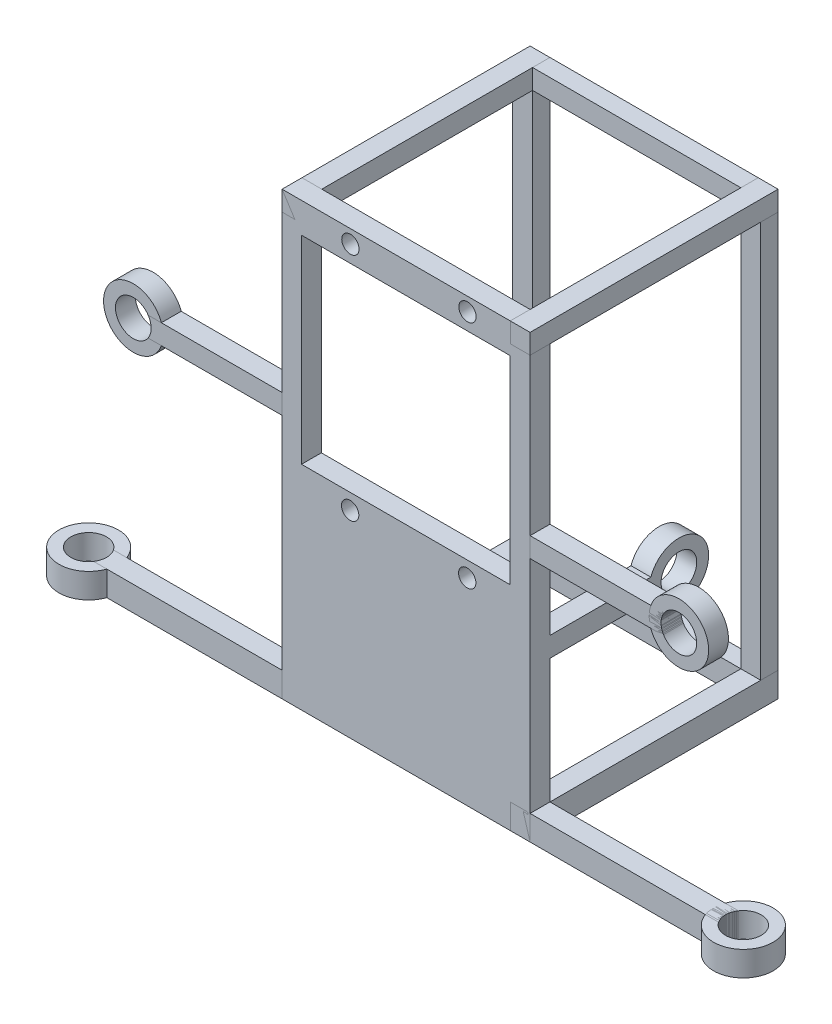
SolidWorks part; units mm, degrees
ref_plane "Front Plane" through (0, 0, 0) normal (0, 0, 1) x (1, 0, 0)
ref_plane "Top Plane" through (0, 0, 0) normal (0, 1, 0) x (1, 0, 0)
ref_plane "Right Plane" through (0, 0, 0) normal (1, 0, 0) x (0, 0, -1)
sketch "Sketch114" plane through (0, 0, 0) normal (1, 0, 0) x (0, 0, -1)
  line L1 (0, 0) -> (3.5, 0)
  line L2 (0, 0) -> (0, 80)
  line L3 (0, 80) -> (3.5, 80)
  line L4 (3.5, 0) -> (3.5, 80)
extrude "Boss-Extrude2" add sketch "Sketch114" along normal blind 4
sketch "Sketch115" plane through (0, 80, 0) normal (0, 1, 0) x (1, 0, 0)
  line L1 (0, 0) -> (50, 0)
  line L2 (0, 0) -> (0, 3.5)
  line L3 (0, 3.5) -> (50, 3.5)
  line L4 (50, 0) -> (50, 3.5)
extrude "Boss-Extrude3" add sketch "Sketch115" along normal blind 4 separate body
sketch "Sketch116" plane through (50, 0, 0) normal (1, 0, 0) x (0, 0, -1)
  line L1 (3.5, 80) -> (0, 80)
  line L2 (3.5, 80) -> (3.5, 0)
  line L3 (3.5, 0) -> (0, 0)
  line L4 (0, 80) -> (0, 0)
extrude "Boss-Extrude5" add sketch "Sketch116" against normal blind 4 separate body
sketch "Sketch117" plane through (0, 0, 0) normal (0, -1, 0) x (1, 0, 0)
  line L0 (0, 0) -> (0, -3.5) construction
  line L1 (0, -3.5) -> (50, -3.5)
  line L2 (0, -3.5) -> (0, 0)
  line L3 (0, 0) -> (50, 0)
  line L4 (50, -3.5) -> (50, 0)
extrude "Boss-Extrude6" add sketch "Sketch117" along normal blind 5 separate body contours L3 L4 L1 L2
sketch "Sketch119" plane through (50, 0, 0) normal (1, 0, 0) x (0, 0, -1)
  line L1 (3.5, -5) -> (-46.5, -5)
  line L2 (3.5, -5) -> (3.5, 0)
  line L3 (3.5, 0) -> (-46.5, 0)
  line L4 (-46.5, -5) -> (-46.5, 0)
  line L5 (3.5, 84) -> (-46.5, 84)
  line L6 (3.5, 84) -> (3.5, 80)
  line L7 (3.5, 80) -> (-46.5, 80)
  line L8 (-46.5, 84) -> (-46.5, 80)
extrude "Boss-Extrude7" add sketch "Sketch119" against normal blind 4 separate body
sketch "Sketch122" plane through (0, 0, 0) normal (-1, 0, 0) x (0, 0, 1)
  line L1 (-3.5, 84) -> (46.5, 84)
  line L2 (-3.5, 84) -> (-3.5, 80)
  line L3 (-3.5, 80) -> (46.5, 80)
  line L4 (46.5, 84) -> (46.5, 80)
  line L5 (-3.5, -5) -> (46.5, -5)
  line L6 (-3.5, -5) -> (-3.5, 0)
  line L7 (-3.5, 0) -> (46.5, 0)
  line L8 (46.5, -5) -> (46.5, 0)
extrude "Boss-Extrude8" add sketch "Sketch122" against normal blind 4 separate body
sketch "Sketch134" plane through (0, 0, 46.5) normal (0, 0, 1) x (1, 0, 0)
  line L1 (0, -5) -> (50, -5)
  line L2 (0, -5) -> (0, 84)
  line L3 (0, 84) -> (50, 84)
  line L4 (50, -5) -> (50, 84)
extrude "Boss-Extrude18" add sketch "Sketch134" against normal blind 4 separate body
sketch "Sketch135" plane through (0, -5, 0) normal (0, -1, 0) x (-1, 0, 0)
  line L1 (-46, -46.5) -> (-91, -46.5)
  line L2 (-46, -46.5) -> (-46, -42.5)
  line L3 (-46, -42.5) -> (-91, -42.5)
  line L4 (-91, -46.5) -> (-91, -42.5)
extrude "Boss-Extrude19" add sketch "Sketch135" against normal blind 5 separate body
sketch "Sketch136" plane through (0, -5, 0) normal (0, -1, 0) x (1, 0, 0)
  line L1 (4, 46.5) -> (-41, 46.5)
  line L2 (4, 46.5) -> (4, 42.5)
  line L3 (4, 42.5) -> (-41, 42.5)
  line L4 (-41, 46.5) -> (-41, 42.5)
extrude "Boss-Extrude21" add sketch "Sketch136" against normal blind 5 separate body
sketch "Sketch137" plane through (0, -5, 0) normal (0, -1, 0) x (1, 0, 0)
  line L0 (91, 42.5) -> (91, 46.5) construction
  circle A0 centre (91, 44.5) radius 6
extrude "Boss-Extrude22" add sketch "Sketch137" against normal blind 5 separate body
sketch "Sketch139" plane through (0, -5, 0) normal (0, -1, 0) x (-1, 0, 0)
  line L0 (-91, -42.5) -> (-91, -46.5) construction
  circle A0 centre (-91, -44.5) radius 3.6
extrude "Cut-Extrude1" cut sketch "Sketch139" against normal blind 38 and the other way blind 10
sketch "Sketch140" plane through (0, -5, 0) normal (0, -1, 0) x (1, 0, 0)
  line L0 (-41, 46.5) -> (-41, 42.5) construction
  circle A0 centre (-41, 44.5) radius 6
extrude "Boss-Extrude23" add sketch "Sketch140" against normal blind 5 separate body
sketch "Sketch143" plane through (0, -5, 0) normal (0, -1, 0) x (1, 0, 0)
  circle A0 centre (-41, 44.5) radius 3.6
extrude "Cut-Extrude2" cut sketch "Sketch143" against normal blind 17 and the other way blind 29
sketch "Sketch145" plane through (0, 5, 42.5) normal (0, 0, -1) x (-1, 0, 0)
  line L1 (0, 39.5) -> (30, 39.5)
  line L2 (0, 39.5) -> (0, 43.5)
  line L3 (0, 43.5) -> (30, 43.5)
  line L4 (30, 39.5) -> (30, 43.5)
extrude "Boss-Extrude26" add sketch "Sketch145" against normal blind 4 separate body contours L4 L3 L2 L1
sketch "Sketch146" plane through (0, 5, 46.5) normal (0, 0, 1) x (1, 0, 0)
  line L0 (-30, 39.5) -> (-30, 43.5) construction
  circle A0 centre (-30, 41.5) radius 6
extrude "Boss-Extrude27" add sketch "Sketch146" against normal blind 4 separate body
sketch "Sketch147" plane through (0, 5, 46.5) normal (0, 0, 1) x (1, 0, 0)
  circle A0 centre (-30, 41.5) radius 3.6
extrude "Cut-Extrude3" cut sketch "Sketch147" against normal blind 21 and the other way blind 11
sketch "Sketch148" plane through (0, 5, 46.5) normal (0, 0, 1) x (1, 0, 0)
  line L1 (50, 39.5) -> (80, 39.5)
  line L2 (50, 39.5) -> (50, 43.5)
  line L3 (50, 43.5) -> (80, 43.5)
  line L4 (80, 39.5) -> (80, 43.5)
extrude "Boss-Extrude28" add sketch "Sketch148" against normal blind 4 separate body
sketch "Sketch149" plane through (0, 5, 42.5) normal (0, 0, -1) x (-1, 0, 0)
  line L0 (-80, 39.5) -> (-80, 43.5) construction
  circle A0 centre (-80, 41.5) radius 6
extrude "Boss-Extrude29" add sketch "Sketch149" against normal blind 4 separate body
sketch "Sketch150" plane through (0, 5, 46.5) normal (0, 0, 1) x (1, 0, 0)
  line L0 (80, 39.5) -> (80, 43.5) construction
  circle A0 centre (80, 41.5) radius 3.6
extrude "Cut-Extrude4" cut sketch "Sketch150" along normal blind 12 and the other way blind 14
sketch "Sketch155" plane through (0, 0, 42.5) normal (0, 0, -1) x (-1, 0, 0)
sketch "Sketch156" plane through (0, 0, 46.5) normal (0, 0, 1) x (1, 0, 0)
  line L1 (3.9148, 77.9202) -> (45.9148, 77.9202)
  line L2 (3.9148, 77.9202) -> (3.9148, -0.0798)
  line L3 (3.9148, -0.0798) -> (45.9148, -0.0798)
  line L4 (45.9148, 77.9202) -> (45.9148, -0.0798)
extrude "Cut-Extrude8" cut sketch "Sketch156" against normal blind 4
sketch "Sketch159" plane through (50, 0, 0) normal (1, 0, 0) x (0, 0, -1)
  line L0 (-46.5, -5) -> (-46.5, 84) construction
  line L1 (-46.5, 29.085) -> (-16.5, 29.085)
  line L2 (-46.5, 29.085) -> (-46.5, 25.085)
  line L3 (-46.5, 25.085) -> (-16.5, 25.085)
  line L4 (-16.5, 29.085) -> (-16.5, 25.085)
extrude "Boss-Extrude31" add sketch "Sketch159" against normal blind 4
sketch "Sketch160" plane through (46, 0, 0) normal (-1, 0, 0) x (0, 0, 1)
  line L0 (16.5, 25.085) -> (16.5, 29.085) construction
  circle A0 centre (16.5, 27.085) radius 6
extrude "Boss-Extrude32" add sketch "Sketch160" against normal blind 4
sketch "Sketch161" plane through (50, 0, 0) normal (1, 0, 0) x (0, 0, -1)
  circle A0 centre (-16.5, 27.085) radius 3.6
extrude "Cut-Extrude10" cut sketch "Sketch161" against normal blind 4
sketch "Sketch162" plane through (0, 0, 46.5) normal (0, 0, 1) x (1, 0, 0)
  line L1 (3.9148, 37.9202) -> (45.9148, 37.9202)
  line L2 (3.9148, 37.9202) -> (3.9148, -4.8929)
  line L7 (3.9148, -4.8929) -> (45.9148, -4.8929)
  line L8 (3.9148, 77.9202) -> (3.9148, -0.0798) construction
  line L13 (45.9148, -0.0798) -> (45.9148, 77.9202) construction
  line L14 (45.9148, 37.9202) -> (45.9148, -4.8929)
  line L15 (45.9148, 77.9202) -> (3.9148, 77.9202) construction
  dimension "D1" = 40
extrude "Boss-Extrude34" add sketch "Sketch162" against normal blind 4
sketch "Sketch163" plane through (0, 0, 46.5) normal (0, 0, 1) x (1, 0, 0)
sketch "Sketch164" plane through (0, 0, 42.5) normal (0, 0, -1) x (-1, 0, 0)
  circle A0 centre (-13.7714, 81.2786) radius 1.75
  circle A1 centre (-37.3714, 81.2786) radius 1.75
  circle A2 centre (-37.3214, 34.7786) radius 1.75
  circle A3 centre (-13.7214, 34.7786) radius 1.75
  dimension "D1" = 23.6
sketch "Sketch165" plane through (0, 37.9202, 0) normal (0, 1, 0) x (1, 0, 0)
extrude "Cut-Extrude12" cut sketch "Sketch164" against normal blind 4
sketch "Sketch166" plane through (0, 31.9202, 0) normal (0, -1, 0) x (1, 0, 0)
